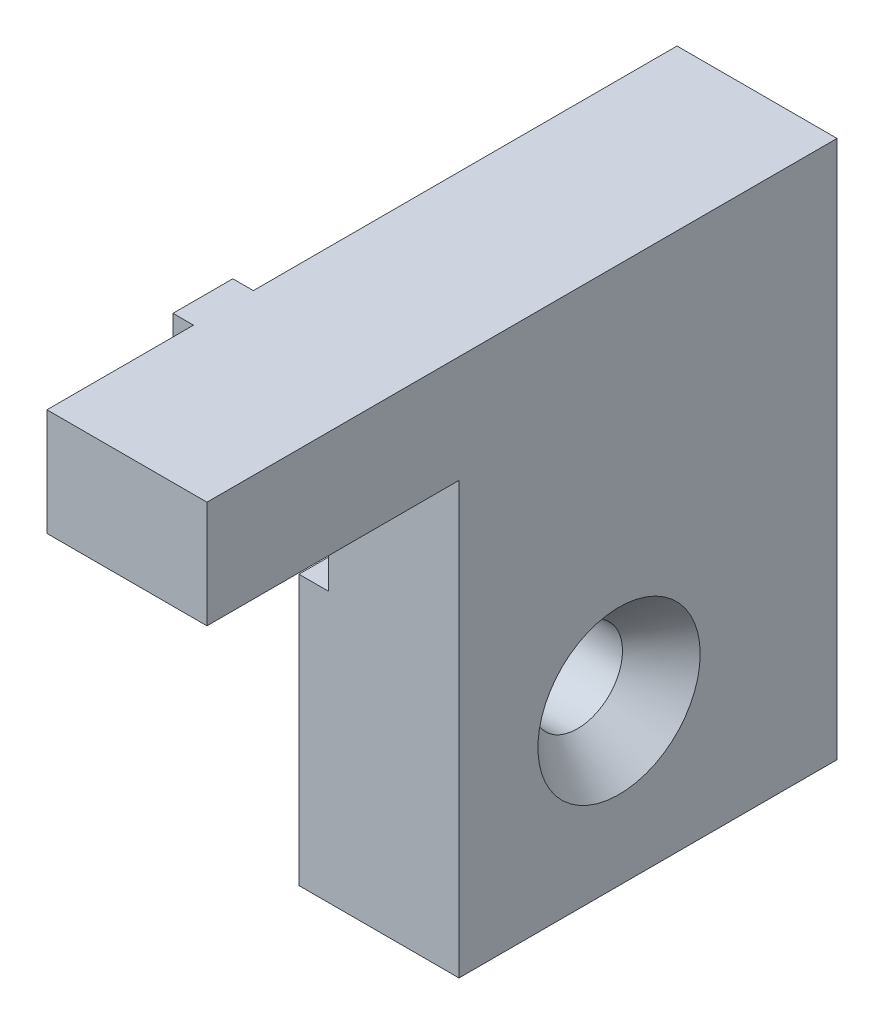
SolidWorks part; units mm, degrees
ref_plane "Front Plane" through (0, 0, 0) normal (0, 0, 1) x (1, 0, 0)
ref_plane "Top Plane" through (0, 0, 0) normal (0, 1, 0) x (1, 0, 0)
ref_plane "Right Plane" through (0, 0, 0) normal (1, 0, 0) x (0, 0, -1)
sketch "Sketch1" plane through (0, 0, 0) normal (1, 0, 0) x (0, 0, -1)
  line L0 (30, -34.2) -> (0, -34.2)
  line L1 (30, -34.2) -> (30, 8.5)
  line L2 (30, 8.5) -> (0, 8.5)
  line L3 (0, -34.2) -> (0, 8.5)
  line L4 (-20, 8.5) -> (0, 8.5)
  line L5 (-20, 8.5) -> (-20, 0)
  line L6 (-20, 0) -> (0, 0)
  line L7 (0, 8.5) -> (0, 0)
  circle A0 centre (12.7, -21.5) radius 3.175
  dimension "D1" = 6.35
  dimension "D2" = 12.7
  dimension "D3" = 12.7
  dimension "D4" = 30
  dimension "D5" = 20
  dimension "D6" = 8.5
  dimension "D7" = 42.7
extrude "Boss-Extrude1" add sketch "Sketch1" along normal blind 12.7 contours L3 L0 L1 L2 A0 | L5 L6 L3 L4
hole_wizard "CSK for 1/4 Flat Head Machine Screw1" positions "3DSketch1" profile "Sketch2" countersink size "1/4" standard "ANSI Inch" end condition through all
sketch3d "3DSketch1"
  line L0 (12.7, -21.5, -12.7) -> (0, -21.5, -12.7) construction
  point P0 (12.7, -21.5, -12.7)
sketch "Sketch2" plane through (12.7, -21.5, -12.7) normal (0, 1, 0) x (0, 0, -1)
  line L0 (0, 0) -> (0, 12.7)
  line L1 (0, 12.7) -> (3.5712, 12.7)
  line L2 (3.5712, 12.7) -> (3.5712, 3.2989)
  line L3 (3.5712, 3.2989) -> (6.4389, 0)
  line L5 (6.4389, 0) -> (0, 0)
  line L6 (-3.5712, 3.2989) -> (-6.4389, 0) construction
  line L11 (0, -6.35) -> (0, 107.95) construction
  dimension "Thru Hole Dia." = 7.1425
  dimension "Thru Hole Depth" = 12.7
  dimension "Near C'Sink Dia." = 12.8778
  dimension "Near C'Sink Angle" = 82
sketch "Sketch3" plane through (0, 0, 0) normal (-1, 0, 0) x (0, 0, 1)
  line L1 (0, 0) -> (-8, 0)
  line L2 (0, 0) -> (0, -12.8)
  line L3 (0, -12.8) -> (-8, -12.8)
  line L4 (-8, 0) -> (-8, -12.8)
  dimension "D1" = 8
  dimension "D2" = 12.8
extrude "Cut-Extrude1" cut sketch "Sketch3" against normal blind 2.35
sketch "Sketch4" plane through (0, 0, 0) normal (-1, 0, 0) x (0, 0, 1)
  line L0 (-30, 8.5) -> (20, 8.5) construction
  line L1 (8.37, 8.5) -> (3.62, 8.5)
  line L2 (8.37, 8.5) -> (8.37, 0)
  line L3 (8.37, 0) -> (3.62, 0)
  line L4 (3.62, 8.5) -> (3.62, 0)
  line L5 (20, 0) -> (-8, 0) construction
  line L6 (20, 8.5) -> (20, 0) construction
  dimension "D1" = 11.63
  dimension "D2" = 4.75
extrude "Boss-Extrude2" add sketch "Sketch4" along normal blind 1.63
